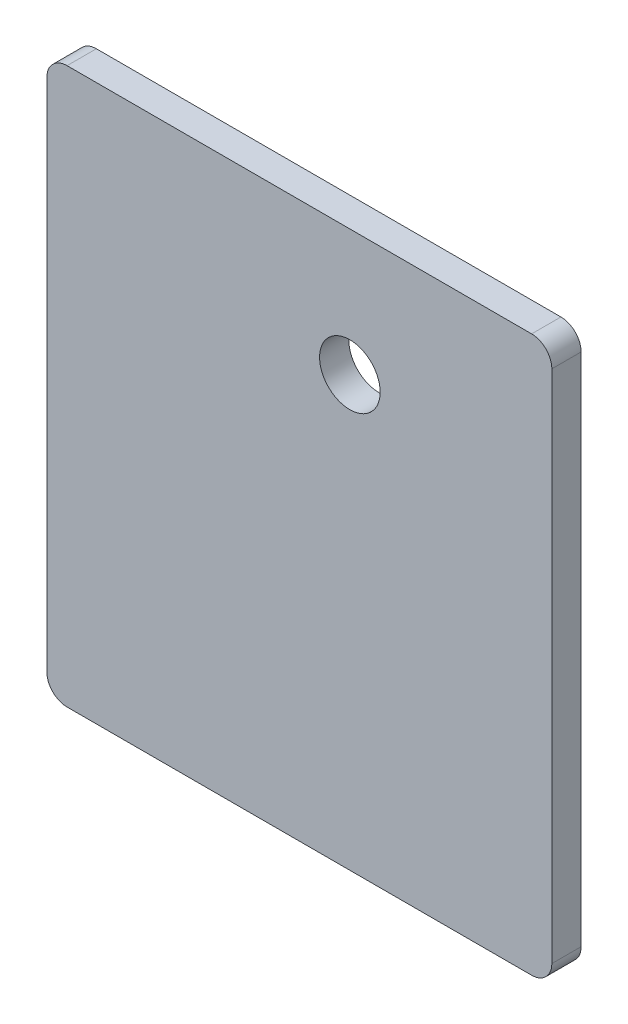
SolidWorks part; units mm, degrees
material "1023 Chapa de acero al carbono (SS)"
ref_plane "Alzado" through (0, 0, 0) normal (0, 0, 1) x (1, 0, 0)
ref_plane "Planta" through (0, 0, 0) normal (0, 1, 0) x (1, 0, 0)
ref_plane "Vista lateral" through (0, 0, 0) normal (1, 0, 0) x (0, 0, -1)
sketch "Croquis1" plane through (0, 0, 0) normal (0, 0, 1) x (1, 0, 0)
  line L1 (0, 0) -> (50, 0)
  line L2 (0, 0) -> (0, 55)
  line L3 (0, 55) -> (50, 55)
  line L4 (50, 0) -> (50, 55)
  circle A0 centre (30, 42.5) radius 3
  dimension "D5" = 6
  dimension "D1" = 55
  dimension "D2" = 50
  dimension "D3" = 42.5
  dimension "D4" = 20
extrude "Saliente-Extruir1" add sketch "Croquis1" along normal blind 2.9
fillet "Redondeo1" radius 2 2 edges at (50, 0, 1.45) (0, 0, 1.45)
fillet "Redondeo2" radius 2 2 edges at (0, 55, 1.45) (50, 55, 1.45)
